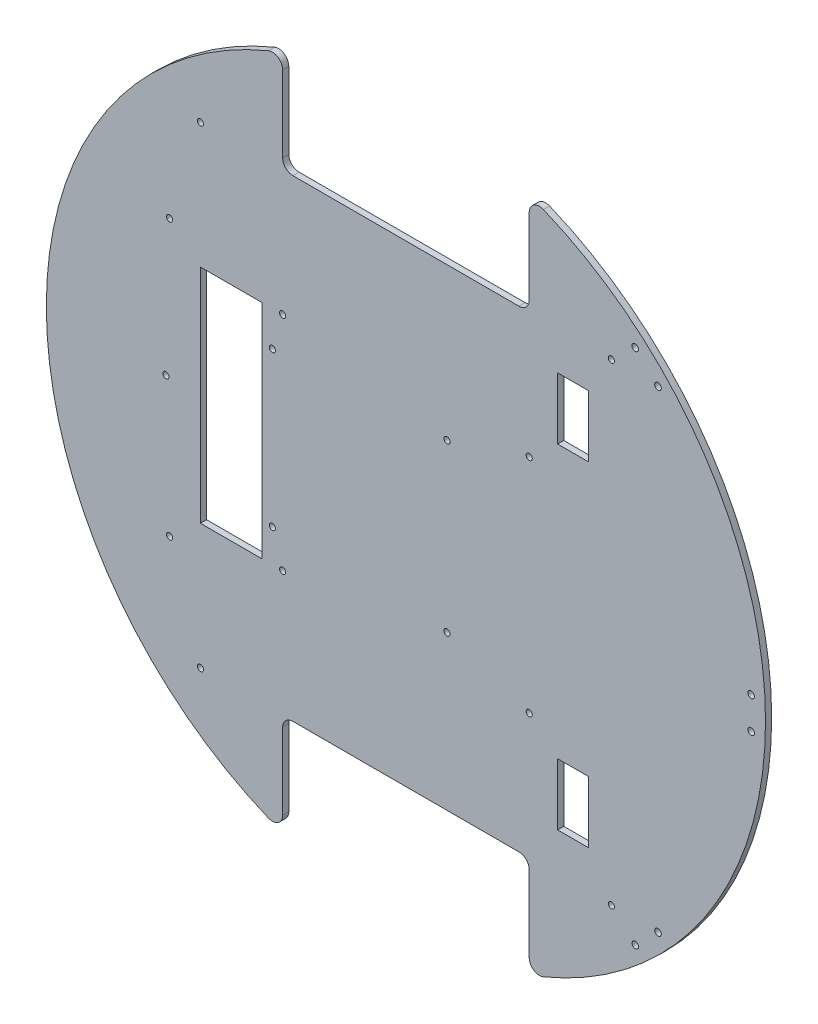
SolidWorks part; units mm, degrees
material "ｱｸﾘﾙ (中-上級の耐衝撃性)"
ref_plane "正面" through (0, 0, 0) normal (0, 0, 1) x (1, 0, 0)
ref_plane "平面" through (0, 0, 0) normal (0, 1, 0) x (1, 0, 0)
ref_plane "右側面" through (0, 0, 0) normal (1, 0, 0) x (0, 0, -1)
sketch "ｽｹｯﾁ1" plane through (0, 0, 0) normal (0, 0, 1) x (1, 0, 0)
  circle A0 centre (0, 0) radius 175
  dimension "D1" = 350
extrude "ﾎﾞｽ - 押し出し1" add sketch "ｽｹｯﾁ1" along normal blind 3
sketch "ｽｹｯﾁ2" plane through (0, 0, 3) normal (0, 0, 1) x (1, 0, 0)
  line L0 (0, 0) -> (175, 0)
  line L1 (0, 0) -> (-175, 0)
  line L2 (0, 0) -> (0, 115)
  line L3 (0, 0) -> (0, -115)
  line L4 (0, 115) -> (60, 115)
  line L5 (0, 115) -> (0, 175)
  line L6 (0, 175) -> (60, 175)
  line L7 (60, 115) -> (60, 175)
  line L8 (0, 115) -> (-60, 115)
  line L9 (0, 115) -> (0, 175)
  line L10 (0, 175) -> (-60, 175)
  line L11 (-60, 115) -> (-60, 175)
  line L13 (0, -115) -> (60, -115)
  line L14 (0, -115) -> (0, -175)
  line L15 (0, -175) -> (60, -175)
  line L16 (60, -115) -> (60, -175)
  line L17 (0, -115) -> (-60, -115)
  line L18 (0, -115) -> (0, -175)
  line L19 (0, -175) -> (-60, -175)
  line L20 (-60, -115) -> (-60, -175)
  circle A0 centre (0, 0) radius 175 construction
  circle M1 centre (0, 0) radius 175
  dimension "D1" = 115
  dimension "D2" = 60
  dimension "D3" = 60
  dimension "D4" = 60
  dimension "D5" = 115
  dimension "D6" = 60
extrude "ｶｯﾄ - 押し出し1" cut sketch "ｽｹｯﾁ2" against normal blind 3 contours L11 L8 L5 M1 | L4 L7 L5 M1 | L17 L20 L14 M1 | L16 L13 L14 M1
fillet "ﾌｨﾚｯﾄ1" radius 5 1 edges at (-60, 164.3928, 1.5)
fillet "ﾌｨﾚｯﾄ2" radius 5 3 edges at (60, 115, 1.5) (60, 164.3928, 1.5) (-60, 115, 1.5)
fillet "ﾌｨﾚｯﾄ3" radius 5 4 edges at (-60, -164.3928, 1.5) (-60, -115, 1.5) (60, -164.3928, 1.5) (60, -115, 1.5)
sketch "ｽｹｯﾁ5" plane through (0, 0, 3) normal (0, 0, 1) x (1, 0, 0)
  line L0 (0, 115) -> (-100, 115)
  line L1 (55, 115) -> (-55, 115) construction
  line L2 (0, 115) -> (100, 115)
  line L3 (0, -115) -> (100, -115)
  line L4 (55, -115) -> (-55, -115) construction
  line L5 (100, -115) -> (-100, -115)
  circle A0 centre (-100, -115) radius 1.5
  circle A1 centre (100, -115) radius 1.5
  circle A2 centre (100, 115) radius 1.5
  circle A3 centre (-100, 115) radius 1.5
  dimension "D3" = 3
  dimension "D4" = 3
  dimension "D5" = 3
  dimension "D6" = 3
  dimension "D1" = 100
  dimension "D2" = 100
extrude "ｶｯﾄ - 押し出し4" cut sketch "ｽｹｯﾁ5" against normal blind 3 contours A1 | A0 | A3 | A2
sketch "ｽｹｯﾁ6" plane through (0, 0, 3) normal (0, 0, 1) x (1, 0, 0)
  line L1 (-60, 54) -> (60, 54)
  line L2 (-60, 54) -> (-60, -54)
  line L3 (-60, -54) -> (60, -54)
  line L4 (60, 54) -> (60, -54)
  line L5 (-60, 54) -> (60, -54) construction
  line L6 (-60, -54) -> (60, 54) construction
  circle A0 centre (-60, 54) radius 1.5
  circle A1 centre (60, 54) radius 1.5
  circle A2 centre (-60, -54) radius 1.5
  circle A3 centre (60, -54) radius 1.5
  point P0 (0, 0)
  dimension "D3" = 3
  dimension "D4" = 3
  dimension "D5" = 3
  dimension "D6" = 3
  dimension "D1" = 120
  dimension "D2" = 108
extrude "ｶｯﾄ - 押し出し5" cut sketch "ｽｹｯﾁ6" against normal blind 3 contours A2 | A0 | A1 | A3
sketch "ｽｹｯﾁ7" plane through (0, 0, 3) normal (0, 0, 1) x (1, 0, 0)
  line L0 (-60, -54) -> (-70, -54)
  line L2 (-70, -54) -> (-100, -54)
  line L3 (-70, -54) -> (-70, 54)
  line L4 (-70, 54) -> (-100, 54)
  line L5 (-100, -54) -> (-100, 54)
  dimension "D1" = 10
  dimension "D2" = 108
  dimension "D3" = 30
extrude "ｶｯﾄ - 押し出し6" cut sketch "ｽｹｯﾁ7" against normal blind 3 contours L5 L2 L3 L4
sketch "ｽｹｯﾁ8" plane through (0, 0, 3) normal (0, 0, 1) x (1, 0, 0)
  line L0 (-100, 0) -> (-115, 0)
  line L1 (-100, -54) -> (-100, 54) construction
  line L2 (-115, 0) -> (-115, 67)
  line L3 (-115, 0) -> (-115, -67)
  circle A0 centre (-115, -67) radius 1.5
  circle A1 centre (-116.8225, 0) radius 1.5
  circle A2 centre (-115, 67) radius 1.5
  dimension "D4" = 3
  dimension "D5" = 3
  dimension "D6" = 3
  dimension "D1" = 15
  dimension "D2" = 67
  dimension "D3" = 67
extrude "ｶｯﾄ - 押し出し7" cut sketch "ｽｹｯﾁ8" against normal blind 3 contours A2 | A1 | A0
sketch "ｽｹｯﾁ9" plane through (0, 0, 3) normal (0, 0, 1) x (1, 0, 0)
  line L0 (-70, 0) -> (-65, 0)
  line L1 (-70, -54) -> (-70, 54) construction
  line L2 (-65, 0) -> (-65, 37)
  line L3 (-65, 37) -> (-64.7716, 37.1905)
  line L4 (-65, 0) -> (-65, -38)
  line L5 (-65, 0) -> (20, 0)
  line L6 (20, 0) -> (20, 41)
  line L7 (20, 0) -> (20, -40)
  circle A0 centre (-65, 37) radius 1.5
  circle A1 centre (20, 41) radius 1.5
  circle A2 centre (-65, -38) radius 1.5
  circle A3 centre (20, -40) radius 1.5
  dimension "D7" = 3
  dimension "D8" = 3
  dimension "D9" = 3
  dimension "D10" = 3
  dimension "D1" = 5
  dimension "D2" = 37
  dimension "D3" = 38
  dimension "D4" = 85
  dimension "D5" = 41
  dimension "D6" = 40
extrude "ｶｯﾄ - 押し出し8" cut sketch "ｽｹｯﾁ9" against normal blind 10 contours A0 | A2 | A1 | A3
sketch "ｽｹｯﾁ10" plane through (0, 0, 3) normal (0, 0, 1) x (1, 0, 0)
  line L0 (0, 0) -> (152.2366, 0)
  line L1 (0, 0) -> (66.9742, 68.8711)
  line L2 (0, 0) -> (76.2283, -78.3873)
  line L3 (175, 0) -> (168, 0)
  line L4 (-175, 0) -> (-168, 0)
  line L5 (66.9742, 68.8711) -> (117.1237, 120.441)
  line L6 (76.2283, -78.3873) -> (117.1237, -120.441)
  line L7 (117.1237, -120.441) -> (122.6798, -115.038)
  line L8 (117.1237, -120.441) -> (111.6437, -125.9211)
  line L9 (168, 0) -> (168, 7.75)
  line L10 (168, 0) -> (168, -7.75)
  line L11 (117.1237, 120.441) -> (111.5677, 125.844)
  line L12 (117.1237, 120.441) -> (122.6798, 115.038)
  arc A0 (66.9118, -161.7029) -> (66.9118, 161.7029) centre (0, 0) ccw construction
  arc A1 (-66.9118, 161.7029) -> (-66.9118, -161.7029) centre (0, 0) ccw construction
  circle A2 centre (0, 0) radius 168
  circle A3 centre (111.6437, -125.9211) radius 1.6
  circle A4 centre (122.6798, -115.038) radius 1.6
  circle A5 centre (168, 7.75) radius 1.6
  circle A6 centre (168, -7.75) radius 1.6
  circle A7 centre (111.5677, 125.844) radius 1.6
  circle A8 centre (122.6798, 115.038) radius 1.6
  dimension "D7" = 3.2
  dimension "D8" = 3.2
  dimension "D11" = 3.2
  dimension "D12" = 3.2
  dimension "D15" = 3.2
  dimension "D16" = 3.2
  dimension "D1" = 45.8
  dimension "D2" = 45.8
  dimension "D3" = 7
  dimension "D4" = 7
  dimension "D5" = 7.75
  dimension "D6" = 7.75
  dimension "D9" = 7.75
  dimension "D10" = 7.75
  dimension "D13" = 7.75
  dimension "D14" = 7.75
extrude "ｶｯﾄ - 押し出し9" cut sketch "ｽｹｯﾁ10" against normal blind 10 contours A3 | A4 | A6 | A5 | A7 | A8
sketch "ｽｹｯﾁ11" plane through (0, 0, 3) normal (0, 0, 1) x (1, 0, 0)
  line L0 (0, 0) -> (115, 0)
  line L1 (0, 0) -> (81.3173, 81.3173)
  line L2 (0, 0) -> (81.3173, -81.3173)
  line L4 (73.8173, 96.3173) -> (88.8173, 96.3173)
  line L5 (73.8173, 96.3173) -> (73.8173, 66.3173)
  line L6 (73.8173, 66.3173) -> (88.8173, 66.3173)
  line L7 (88.8173, 96.3173) -> (88.8173, 66.3173)
  line L8 (73.8173, 96.3173) -> (88.8173, 66.3173) construction
  line L9 (73.8173, 66.3173) -> (88.8173, 96.3173) construction
  line L10 (73.8173, -66.3173) -> (88.8173, -66.3173)
  line L11 (73.8173, -66.3173) -> (73.8173, -96.3173)
  line L12 (73.8173, -96.3173) -> (88.8173, -96.3173)
  line L13 (88.8173, -66.3173) -> (88.8173, -96.3173)
  line L14 (73.8173, -66.3173) -> (88.8173, -96.3173) construction
  line L15 (73.8173, -96.3173) -> (88.8173, -66.3173) construction
  circle A0 centre (0, 0) radius 115
  dimension "D1" = 230
  dimension "D2" = 45
  dimension "D3" = 45
  dimension "D4" = 30
  dimension "D5" = 15
  dimension "D6" = 15
  dimension "D7" = 30
extrude "ｶｯﾄ - 押し出し10" cut sketch "ｽｹｯﾁ11" against normal blind 10 contours L7 L6 L5 L4 | L13 L12 L11 L10
